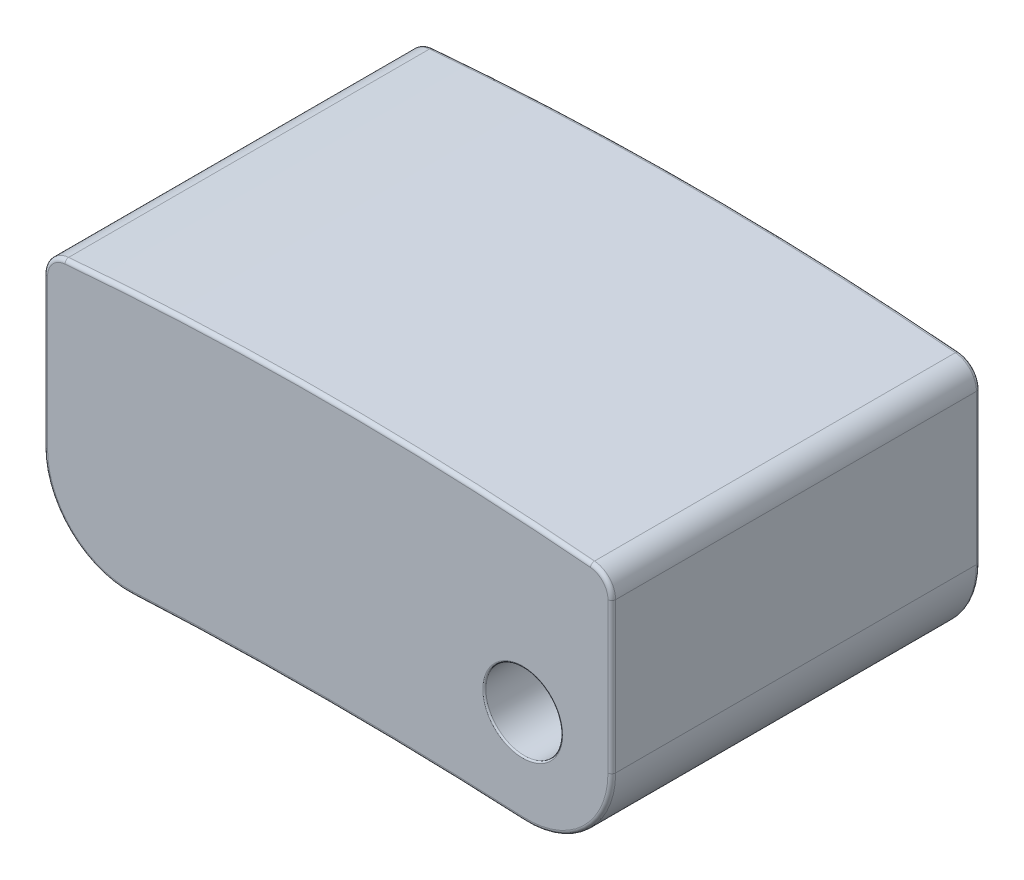
SolidWorks part; units mm, degrees
ref_plane "Front Plane" through (0, 0, 0) normal (0, 0, 1) x (1, 0, 0)
ref_plane "Top Plane" through (0, 0, 0) normal (0, 1, 0) x (1, 0, 0)
ref_plane "Right Plane" through (0, 0, 0) normal (1, 0, 0) x (0, 0, -1)
sketch "Sketch1" plane through (0, 0, 0) normal (0, 0, 1) x (1, 0, 0)
  line L0 (55, 0) -> (-55, 0) construction
  line L1 (-3.7, 1.85) -> (3.7, 1.85)
  line L2 (-3.7, 1.85) -> (-3.7, -1.85)
  line L3 (-3.7, -1.85) -> (3.7, -1.85)
  line L4 (3.7, 1.85) -> (3.7, -1.85)
  line L5 (0, -55) -> (0, 55) construction
  dimension "D1" = 7.4
  dimension "D2" = 3.7
  dimension "D3" = 1.85
  dimension "D4" = 3.7
extrude "Boss-Extrude1" add sketch "Sketch1" along normal mid plane 4.8
sketch "Sketch2" plane through (0, 0, 2.4) normal (0, 0, 1) x (1, 0, 0)
  line L0 (-3.7, 1.85) -> (-3.7, -1.85) construction
  line L1 (3.7, -1.85) -> (3.7, 1.85) construction
  line L2 (-3.7, -1.85) -> (3.7, -1.85) construction
  line L3 (3.7, 1.85) -> (-3.7, 1.85) construction
  line L4 (-3.7, 1.55) -> (-7.1207, 4.0114)
  line L5 (-7.1207, 4.0114) -> (5.5359, 3.8867)
  line L6 (5.5359, 3.8867) -> (3.7, 1.55)
  line L7 (3.7, -1.85) -> (0.3506, -3.782)
  line L8 (-3.7, -1.85) -> (0.3506, -3.782)
  arc A0 (-3.7, 1.55) -> (3.7, 1.55) centre (0, -38.2785) cw
  arc A1 (-3.7, -1.85) -> (3.7, -1.85) centre (0, -51.7129) cw
  dimension "D4" = 40
  dimension "D5" = 50
  dimension "D1" = 0
  dimension "D2" = 0.3
  dimension "D3" = 0.3
extrude "Cut-Extrude1" cut sketch "Sketch2" against normal blind 4.8
fillet "Fillet1" radius 1.1 2 edges at (3.7, -1.85, 0) (-3.7, -1.85, 0)
fillet "Fillet2" radius 0.3 2 edges at (3.7, 1.55, 0) (-3.7, 1.55, 0)
fillet "Fillet3" radius 0.05 16 edges at (-3.621, 1.4785, -2.4) (-3.7, 0.2983, -2.4) (-3.3578, -1.4765, -2.4) (0, -1.7129, -2.4) (3.3578, -1.4765, -2.4) (3.7, 0.2983, -2.4) (3.621, 1.4785, -2.4) (0, 1.7215, -2.4) (3.3578, -1.4765, 2.4) (0, -1.7129, 2.4) (-3.3578, -1.4765, 2.4) (-3.7, 0.2983, 2.4) (-3.621, 1.4785, 2.4) (0, 1.7215, 2.4) (3.621, 1.4785, 2.4) (3.7, 0.2983, 2.4)
sketch "Sketch3" plane through (0, 0, 2.4) normal (0, 0, 1) x (1, 0, 0)
  circle A0 centre (2.5394, -0.5484) radius 0.5
  dimension "D1" = 1
extrude "Cut-Extrude2" cut sketch "Sketch3" against normal mid plane 14.8 from offset 1 offset against normal yes
fillet "Fillet4" radius 0.02 2 edges at (3.0394, -0.5484, -2.4) (3.0394, -0.5484, 2.4)
sketch "Sketch4" plane through (0, 0, -2.4) normal (0, 0, -1) x (-1, 0, 0)
  line L0 (2.64, 0) -> (-2.64, 0) construction
  line L1 (0, 1.9253) -> (0, -1.9253) construction
  circle A0 centre (2, -0.5) radius 0.5
  dimension "D1" = 1
  dimension "D2" = 0.5
  dimension "D3" = 2
extrude "Cut-Extrude3" cut sketch "Sketch4" against normal blind 4.5 from offset 1
sketch "Sketch5" plane through (0, 0, 0) normal (0, 1, 0) x (1, 0, 0)
  line L0 (2.5466, 2.4) -> (-2.5466, 2.4) construction
  line L1 (3.7, -2.35) -> (3.7, 2.35) construction
  circle A0 centre (0.7, 1) radius 0.4
  dimension "D1" = 0.8
  dimension "D3" = 3
  dimension "D2" = 1.4
extrude "Cut-Extrude4" cut sketch "Sketch5" along normal offset from surface (8.6822 mm away) 0.4 from offset 10 offset against normal yes
fillet "Fillet5" radius 0.05 1 edges at (0.608, -1.7166, -0.6107)
